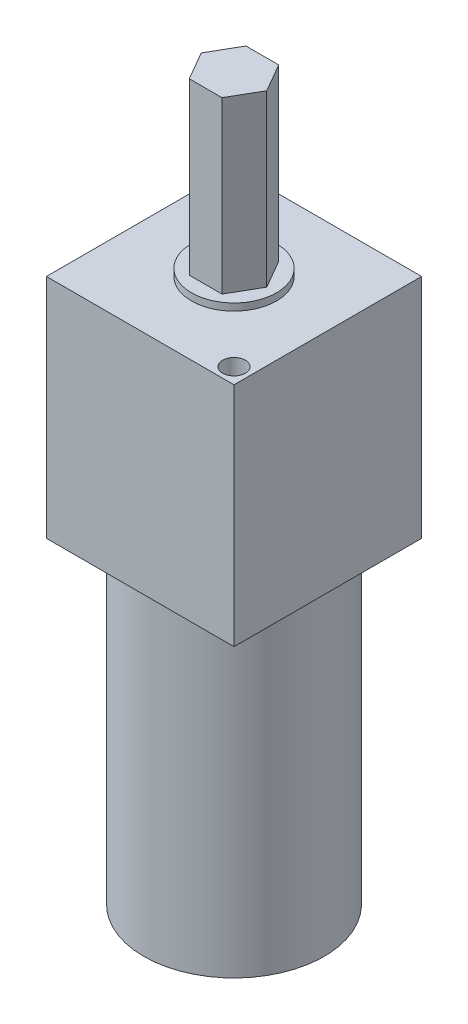
SolidWorks part; units mm, degrees
ref_plane "Front Plane" through (0, 0, 0) normal (0, 0, 1) x (1, 0, 0)
ref_plane "Top Plane" through (0, 0, 0) normal (0, 1, 0) x (1, 0, 0)
ref_plane "Right Plane" through (0, 0, 0) normal (1, 0, 0) x (0, 0, -1)
sketch "Sketch1" plane through (0, 0, 0) normal (0, 1, 0) x (1, 0, 0)
  line L1 (-21.0058, 21.0058) -> (21.0058, 21.0058)
  line L2 (-21.0058, 21.0058) -> (-21.0058, -21.0058)
  line L3 (-21.0058, -21.0058) -> (21.0058, -21.0058)
  line L4 (21.0058, 21.0058) -> (21.0058, -21.0058)
  line L5 (-21.0058, 21.0058) -> (21.0058, -21.0058) construction
  line L6 (-21.0058, -21.0058) -> (21.0058, 21.0058) construction
  circle A0 centre (0, 0) radius 24.7523 construction
  circle A1 centre (-17.5025, 17.5025) radius 2.54
  circle A2 centre (17.5025, -17.5025) radius 2.54
  point P0 (0, 0)
  dimension "D1" = 49.5046
  dimension "D2" = 5.08
  dimension "D3" = 42.0116
  dimension "D4" = 42.0116
extrude "Boss-Extrude1" add sketch "Sketch1" along normal blind 50.8
sketch "Sketch2" plane through (0, 50.8, 0) normal (0, 1, 0) x (1, 0, 0)
  circle A0 centre (0, 0) radius 9.525
  dimension "D1" = 19.05
extrude "Boss-Extrude2" add sketch "Sketch2" along normal blind 1.5875
sketch "Sketch3" plane through (0, 52.3875, 0) normal (0, 1, 0) x (1, 0, 0)
  line L1 (3.6662, -6.35) -> (7.3323, 0)
  line L2 (7.3323, 0) -> (3.6662, 6.35)
  line L3 (3.6662, 6.35) -> (-3.6662, 6.35)
  line L4 (-3.6662, 6.35) -> (-7.3323, 0)
  line L5 (-7.3323, 0) -> (-3.6662, -6.35)
  line L6 (-3.6662, -6.35) -> (3.6662, -6.35)
  circle A0 centre (0, 0) radius 6.35 construction
  dimension "D1" = 12.7
extrude "Boss-Extrude3" add sketch "Sketch3" along normal blind 38.1
sketch "Sketch4" plane through (0, 0, 0) normal (0, -1, 0) x (1, 0, 0)
  circle A0 centre (0, 0) radius 20.193
  dimension "D1" = 40.386
extrude "Boss-Extrude4" add sketch "Sketch4" along normal blind 70.993
